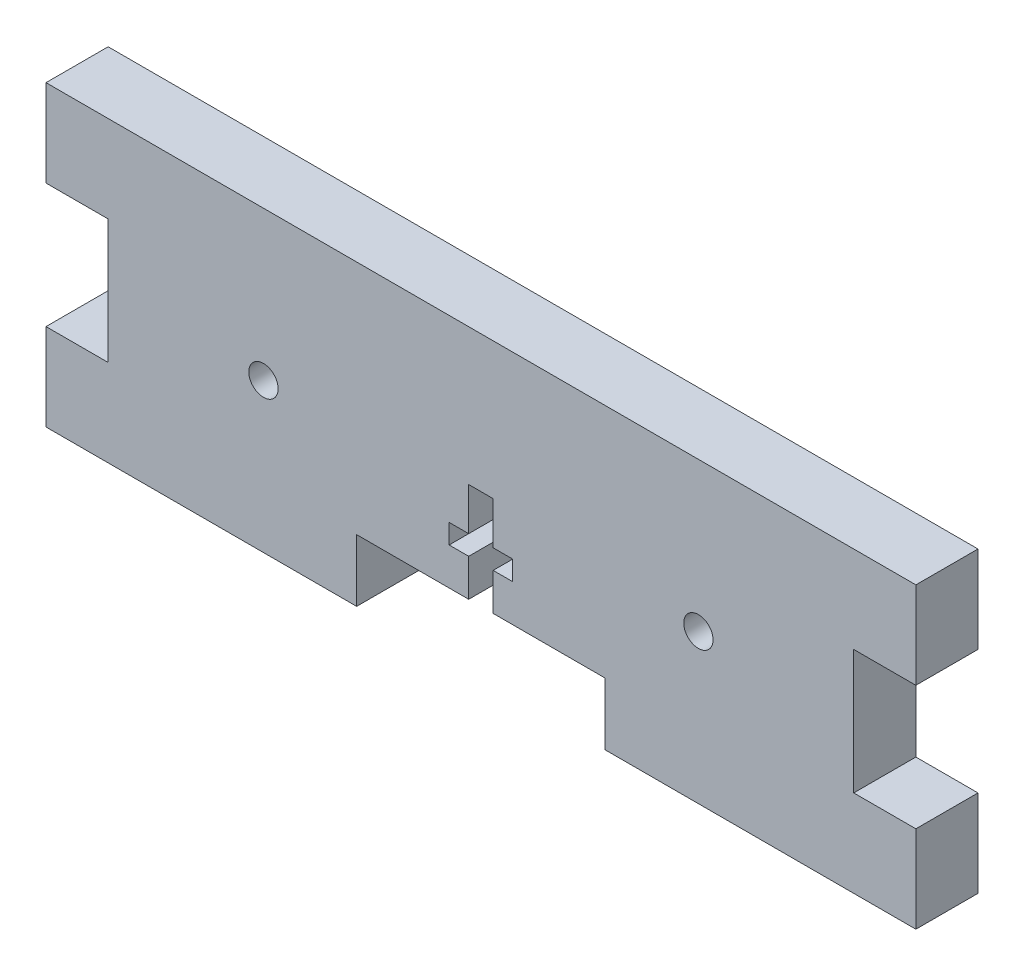
SolidWorks part; units mm, degrees
ref_plane "Front Plane" through (0, 0, 0) normal (0, 0, 1) x (1, 0, 0)
ref_plane "Top Plane" through (0, 0, 0) normal (0, 1, 0) x (1, 0, 0)
ref_plane "Right Plane" through (0, 0, 0) normal (1, 0, 0) x (0, 0, -1)
sketch "Sketch1" plane through (0, 0, 0) normal (0, 0, 1) x (1, 0, 0)
  line L0 (0, 21.59) -> (0, 30.48)
  line L1 (0, 0) -> (88.9, 0)
  line L2 (0, 0) -> (0, 8.89)
  line L3 (0, 30.48) -> (88.9, 30.48)
  line L4 (88.9, 0) -> (88.9, 8.89)
  line L5 (0, 21.59) -> (6.35, 21.59)
  line L6 (88.9, 21.59) -> (88.9, 30.48)
  line L7 (0, 8.89) -> (6.35, 8.89)
  line L8 (6.35, 21.59) -> (6.35, 8.89)
  line L9 (88.9, 21.59) -> (82.55, 21.59)
  line L11 (88.9, 8.89) -> (82.55, 8.89)
  line L12 (82.55, 21.59) -> (82.55, 8.89)
  dimension "D1" = 88.9
  dimension "D2" = 30.48
  dimension "D3" = 6.35
  dimension "D4" = 12.7
extrude "Boss-Extrude1" add sketch "Sketch1" along normal blind 6.35
sketch "Sketch2" plane through (0, 0, 6.35) normal (0, 0, 1) x (1, 0, 0)
  line L0 (0, 0) -> (88.9, 0) construction
  line L1 (31.75, 0) -> (57.15, 0)
  line L2 (31.75, 0) -> (31.75, 6.35)
  line L3 (31.75, 6.35) -> (57.15, 6.35)
  line L4 (57.15, 0) -> (57.15, 6.35)
  line L5 (31.75, 3.175) -> (0, 3.175) construction
  line L7 (57.15, 3.175) -> (88.9, 3.175) construction
  line L8 (88.9, 0) -> (88.9, 8.89) construction
  line L9 (0, 8.89) -> (0, 0) construction
  line L10 (6.35, 15.24) -> (22.225, 15.24) construction
  line L11 (6.35, 21.59) -> (6.35, 8.89) construction
  line L12 (22.225, 15.24) -> (66.675, 15.24) construction
  line L13 (66.675, 15.24) -> (82.55, 15.24) construction
  line L14 (82.55, 8.89) -> (82.55, 21.59) construction
  circle A0 centre (22.225, 15.24) radius 1.5
  circle A1 centre (66.675, 15.24) radius 1.5
  dimension "D3" = 3
  dimension "D1" = 25.4
  dimension "D2" = 6.35
  dimension "D4" = 44.45
extrude "Cut-Extrude1" cut sketch "Sketch2" against normal through all
sketch "Sketch3" plane through (0, 0, 6.35) normal (0, 0, 1) x (1, 0, 0)
  line L0 (57.15, 6.35) -> (31.75, 6.35) construction
  line L3 (43.2, 6.35) -> (45.7, 6.35)
  line L4 (43.2, 6.35) -> (43.2, 10.16)
  line L5 (43.2, 16.51) -> (45.7, 16.51)
  line L6 (45.7, 6.35) -> (45.7, 10.16)
  line L8 (44.45, 6.35) -> (44.45, 16.51) construction
  line L9 (43.2, 12.16) -> (41.2, 12.16)
  line L10 (45.7, 12.16) -> (45.7, 16.51)
  line L11 (43.2, 10.16) -> (41.2, 10.16)
  line L12 (41.2, 12.16) -> (41.2, 10.16)
  line L13 (45.7, 12.16) -> (47.7, 12.16)
  line L15 (45.7, 10.16) -> (47.7, 10.16)
  line L16 (47.7, 12.16) -> (47.7, 10.16)
  line L17 (43.2, 12.16) -> (43.2, 16.51)
extrude "Cut-Extrude2" cut sketch "Sketch3" against normal through all contours L17 L5 L10 L13 L16 L15 L6 L3 L4 L11 L12 L9
